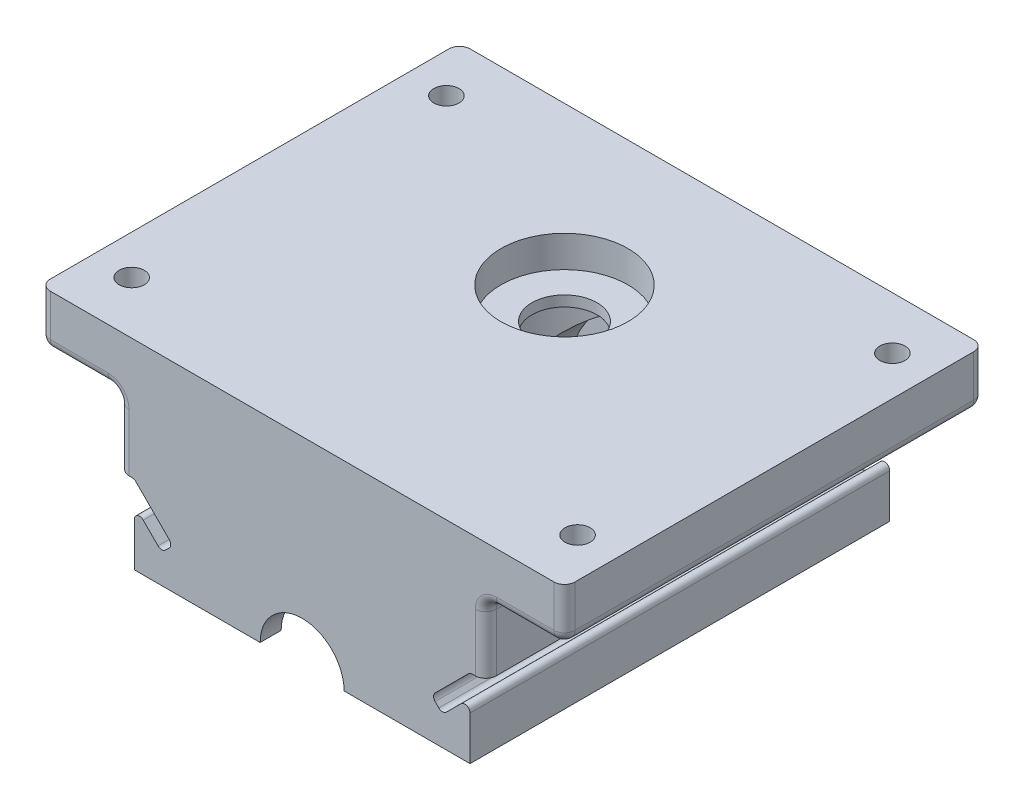
SolidWorks part; units mm, degrees
ref_plane "Plan de face" through (0, 0, 0) normal (0, 0, 1) x (1, 0, 0)
ref_plane "Plan de dessus" through (0, 0, 0) normal (0, 1, 0) x (1, 0, 0)
ref_plane "Plan de droite" through (0, 0, 0) normal (1, 0, 0) x (0, 0, -1)
sketch "Esquisse1" plane through (0, 0, 0) normal (0, 1, 0) x (1, 0, 0)
  line L1 (0, 0) -> (100, 0)
  line L2 (0, 0) -> (0, 80)
  line L3 (0, 80) -> (100, 80)
  line L4 (100, 0) -> (100, 80)
  dimension "D1" = 80
  dimension "D2" = 100
extrude "Boss.-Extru.1" add sketch "Esquisse1" along normal blind 10
sketch "Esquisse2" plane through (0, 0, 0) normal (0, -1, 0) x (1, 0, 0)
  line L0 (0, -80) -> (100, -80) construction
  line L1 (15, -80) -> (85, -80)
  line L2 (15, -80) -> (15, 0)
  line L3 (15, 0) -> (85, 0)
  line L4 (85, -80) -> (85, 0)
  line L5 (0, 0) -> (100, 0) construction
  line L6 (0, 0) -> (0, -80) construction
  dimension "D1" = 15
  dimension "D2" = 70
extrude "Boss.-Extru.2" add sketch "Esquisse2" along normal blind 28
sketch "Esquisse11" plane through (0, 0, -80) normal (0, 0, -1) x (-1, 0, 0)
  line L0 (-15, -28) -> (-85, -28) construction
  line L1 (-15, -28) -> (-85, -28)
  line L2 (-15, -28) -> (-85, -28) construction
  circle A0 centre (-50, -28) radius 20
  point P7 (-50, -28)
  dimension "D1" = 40
extrude "Boss.-Extru.3" add sketch "Esquisse11" along normal blind 6.15 contours L1 A0
sketch "Esquisse3" plane through (0, -28, -30) normal (0, 1, 0) x (1, 0, 0)
  line L0 (50, 56.15) -> (50, -30)
  line L4 (50, 52.15) -> (62, 52.15)
  line L5 (50, 52.15) -> (50, 45.95)
  line L6 (50, 45.95) -> (62, 45.95)
  line L7 (62, 52.15) -> (62, 45.95)
  line L8 (50, 45.95) -> (58, 45.95)
  line L9 (50, 45.95) -> (50, 41.95)
  line L10 (50, 41.95) -> (58, 41.95)
  line L11 (58, 45.95) -> (58, 41.95)
  line L12 (50, 41.95) -> (71.5, 41.95)
  line L13 (50, 41.95) -> (50, -15.8)
  line L14 (50, -15.8) -> (71.5, -15.8)
  line L15 (71.5, 41.95) -> (71.5, -15.8)
  line L16 (50, -19.8) -> (58, -19.8)
  line L17 (50, -19.8) -> (50, -15.8)
  line L18 (50, -15.8) -> (58, -15.8)
  line L19 (58, -19.8) -> (58, -15.8)
  line L20 (50, -26) -> (62, -26)
  line L21 (50, -26) -> (50, -19.8)
  line L22 (50, -19.8) -> (62, -19.8)
  line L23 (62, -26) -> (62, -19.8)
  line L24 (50, -30) -> (58, -30)
  line L25 (50, -30) -> (50, -26)
  line L26 (50, -26) -> (58, -26)
  line L27 (58, -30) -> (58, -26)
  line L31 (15, 50) -> (15, -30)
  line L32 (30, 50) -> (15, 50)
  line L33 (85, -30) -> (85, 50)
  line L34 (15, -30) -> (85, -30)
  line L35 (15, 50) -> (15, -30)
  line L36 (30, 50) -> (15, 50)
  line L37 (85, -30) -> (85, 50)
  line L38 (15, -30) -> (85, -30)
  line L42 (30, 56.15) -> (30, 50)
  line L43 (30, 56.15) -> (30, 50)
  line L44 (70, 56.15) -> (30, 56.15)
  line L45 (70, 56.15) -> (30, 56.15)
  line L46 (70, 50) -> (70, 56.15)
  line L47 (70, 50) -> (70, 56.15)
  line L48 (85, 50) -> (70, 50)
  line L49 (85, 50) -> (70, 50)
  line L50 (15, 50) -> (15, -30)
  line L51 (30, 50) -> (15, 50)
  line L52 (30, 56.15) -> (30, 50)
  line L53 (70, 56.15) -> (30, 56.15)
  line L54 (70, 50) -> (70, 56.15)
  line L55 (85, 50) -> (70, 50)
  line L56 (85, -30) -> (85, 50)
  line L57 (15, -30) -> (85, -30)
  line L58 (15, 50) -> (15, -30)
  line L59 (30, 50) -> (15, 50)
  line L60 (30, 56.15) -> (30, 50)
  line L61 (70, 56.15) -> (30, 56.15)
  line L62 (70, 50) -> (70, 56.15)
  line L63 (85, 50) -> (70, 50)
  line L64 (85, -30) -> (85, 50)
  line L65 (15, -30) -> (85, -30)
  point P44 (50, -30)
  dimension "D2" = 6.2
  dimension "D3" = 12
  dimension "D4" = 4
  dimension "D5" = 8
  dimension "D6" = 4
  dimension "D7" = 4
  dimension "D8" = 8
  dimension "D9" = 6.2
  dimension "D10" = 12
  dimension "D11" = 8
  dimension "D12" = 21.5
  dimension "D14" = 0
  dimension "D15" = 4
  dimension "D13" = 0
revolve "Enlèvement de matière-Révolution1" cut sketch "Esquisse3" angle 360 about L0
sketch "Esquisse4" plane through (0, -28, 0) normal (0, -1, 0) x (-1, 0, 0)
  line L0 (-58, 0) -> (-58, 4) construction
  line L1 (-58, 4) -> (-62, 4) construction
  line L2 (-62, 4) -> (-62, 10.2) construction
  line L3 (-62, 10.2) -> (-58, 10.2) construction
  line L4 (-58, 10.2) -> (-58, 14.2) construction
  line L5 (-58, 14.2) -> (-71.5, 14.2) construction
  line L6 (-71.5, 71.95) -> (-58, 71.95) construction
  line L7 (-58, 71.95) -> (-58, 75.95) construction
  line L8 (-58, 75.95) -> (-62, 75.95) construction
  line L9 (-62, 75.95) -> (-62, 82.15) construction
  line L10 (-62, 82.15) -> (-38, 82.15) construction
  line L11 (-38, 82.15) -> (-38, 75.95) construction
  line L12 (-38, 75.95) -> (-42, 75.95) construction
  line L13 (-42, 75.95) -> (-42, 71.95) construction
  line L14 (-42, 71.95) -> (-28.5, 71.95) construction
  line L15 (-28.5, 14.2) -> (-42, 14.2) construction
  line L16 (-42, 14.2) -> (-42, 10.2) construction
  line L17 (-42, 10.2) -> (-38, 10.2) construction
  line L18 (-38, 10.2) -> (-38, 4) construction
  line L19 (-38, 4) -> (-42, 4) construction
  line L20 (-42, 4) -> (-42, 0) construction
  line L21 (-42, 0) -> (-15, 0) construction
  line L22 (-15, 0) -> (-15, 80) construction
  line L23 (-50, 14.2) -> (-50, 86.15)
  line L24 (-85, 80) -> (-85, 0) construction
  line L25 (-85, 0) -> (-58, 0) construction
  line L26 (-28.5, 14.2) -> (-71.5, 14.2) construction
  line L27 (-71.5, 71.95) -> (-28.5, 71.95) construction
  line L28 (-58, 0) -> (-58, 4)
  line L29 (-58, 4) -> (-62, 4)
  line L30 (-62, 4) -> (-62, 10.2)
  line L31 (-62, 10.2) -> (-58, 10.2)
  line L32 (-58, 10.2) -> (-58, 14.2)
  line L33 (-58, 14.2) -> (-71.5, 14.2)
  line L34 (-71.5, 71.95) -> (-58, 71.95)
  line L35 (-58, 71.95) -> (-58, 75.95)
  line L36 (-58, 75.95) -> (-62, 75.95)
  line L37 (-62, 75.95) -> (-62, 82.15)
  line L38 (-62, 82.15) -> (-38, 82.15)
  line L39 (-38, 82.15) -> (-38, 75.95)
  line L40 (-38, 75.95) -> (-42, 75.95)
  line L41 (-42, 75.95) -> (-42, 71.95)
  line L42 (-42, 71.95) -> (-28.5, 71.95)
  line L43 (-28.5, 14.2) -> (-42, 14.2)
  line L44 (-42, 14.2) -> (-42, 10.2)
  line L45 (-42, 10.2) -> (-38, 10.2)
  line L46 (-38, 10.2) -> (-38, 4)
  line L47 (-38, 4) -> (-42, 4)
  line L48 (-42, 4) -> (-42, 0)
  line L49 (-42, 0) -> (-15, 0)
  line L50 (-15, 0) -> (-15, 80)
  line L51 (-15, 80) -> (-85, 80)
  line L52 (-85, 80) -> (-85, 0)
  line L53 (-85, 0) -> (-58, 0)
  line L54 (-28.5, 14.2) -> (-71.5, 14.2)
  line L55 (-71.5, 71.95) -> (-28.5, 71.95)
  line L57 (-30, 86.15) -> (-30, 80) construction
  line L58 (-70, 86.15) -> (-30, 86.15) construction
  line L59 (-70, 86.15) -> (-70, 80) construction
  line L60 (-30, 86.15) -> (-30, 80)
  line L61 (-70, 86.15) -> (-30, 86.15)
  line L62 (-70, 86.15) -> (-70, 80)
  circle A0 centre (-50, 50) radius 21
  dimension "D1" = 42
  dimension "D2" = 30
extrude "Enlèv. mat.-Extru.1" cut sketch "Esquisse4" against normal blind 30
sketch "Esquisse5" plane through (0, 10, 0) normal (0, 1, 0) x (1, 0, 0)
  line L0 (50, 80) -> (50, 0)
  line L4 (0, 0) -> (100, 0)
  line L5 (100, 0) -> (100, 80)
  line L6 (100, 80) -> (0, 80)
  line L7 (0, 80) -> (0, 0)
  line L8 (0, 0) -> (100, 0)
  line L9 (100, 0) -> (100, 80)
  line L10 (100, 80) -> (0, 80)
  line L11 (0, 80) -> (0, 0)
  circle A0 centre (50, 50) radius 12.1
  dimension "D2" = 24.2
  dimension "D3" = 30
  dimension "D1" = 0
extrude "Enlèv. mat.-Extru.2" cut sketch "Esquisse5" against normal blind 6
sketch "Esquisse6" plane through (0, 4, 0) normal (0, 1, 0) x (1, 0, 0)
  circle A0 centre (50, 50) radius 6.2
  circle A1 centre (50, 50) radius 12.1
  circle A2 centre (50, 50) radius 12.1
  dimension "D2" = 12.4
  dimension "D1" = 0
extrude "Enlèv. mat.-Extru.3" cut sketch "Esquisse6" against normal through all contours A0
sketch "Esquisse7" plane through (0, 0, 0) normal (0, 0, 1) x (1, 0, 0)
  line L0 (18.2929, -13.2929) -> (24.6569, -19.6569)
  line L1 (15, -28) -> (18, -28)
  line L2 (15, -28) -> (15, -13)
  line L3 (15, -13) -> (17.5858, -13)
  line L4 (18, -28) -> (18, -19.6569)
  line L5 (18, -13) -> (25.364, -20.364)
  line L7 (24.6569, -21.0711) -> (23.9497, -21.7782)
  line L8 (19.7071, -18.9497) -> (22.5355, -21.7782)
  line L9 (58, -28) -> (85, -28)
  line L10 (85, -28) -> (85, 0)
  line L11 (85, 0) -> (100, 0)
  line L12 (100, 0) -> (100, 10)
  line L13 (100, 10) -> (0, 10)
  line L14 (0, 10) -> (0, 0)
  line L15 (0, 0) -> (15, 0)
  line L16 (15, 0) -> (15, -28)
  line L17 (15, -28) -> (42, -28)
  line L18 (58, -28) -> (85, -28)
  line L20 (85, 0) -> (100, 0)
  line L21 (100, 0) -> (100, 10)
  line L22 (100, 10) -> (0, 10)
  line L23 (0, 10) -> (0, 0)
  line L24 (0, 0) -> (15, 0)
  line L25 (15, 0) -> (15, -28)
  line L26 (15, -28) -> (42, -28)
  line L27 (50, -33) -> (50, -25)
  line L28 (82, -28) -> (82, -19.6569)
  line L29 (80.2929, -18.9497) -> (77.4645, -21.7782)
  line L30 (75.3431, -21.0711) -> (76.0503, -21.7782)
  line L31 (81.7071, -13.2929) -> (75.3431, -19.6569)
  line L32 (85, -13) -> (82.4142, -13)
  arc A0 (24.6569, -19.6569) -> (24.6569, -21.0711) centre (23.9497, -20.364) cw
  arc A1 (58, -28) -> (42, -28) centre (50, -28) ccw
  arc A3 (23.9497, -21.7782) -> (22.5355, -21.7782) centre (23.2426, -21.0711) cw
  arc A4 (19.7071, -18.9497) -> (18, -19.6569) centre (19, -19.6569) ccw
  arc A5 (80.2929, -18.9497) -> (82, -19.6569) centre (81, -19.6569) cw
  arc A6 (76.0503, -21.7782) -> (77.4645, -21.7782) centre (76.7574, -21.0711) ccw
  arc A7 (75.3431, -19.6569) -> (75.3431, -21.0711) centre (76.0503, -20.364) ccw
  arc A8 (18.2929, -13.2929) -> (17.5858, -13) centre (17.5858, -14) ccw
  arc A9 (81.7071, -13.2929) -> (82.4142, -13) centre (82.4142, -14) cw
  arc A11 (58, -28) -> (42, -28) centre (50, -28) ccw
  point P43 (82, -13)
  dimension "D7" = 1
  dimension "D8" = 1
  dimension "D3" = 1
  dimension "D11" = 1
  dimension "D2" = 15
  dimension "D4" = 9
  dimension "D5" = 45
  dimension "D6" = 3
  dimension "D9" = 8.3431
  dimension "D10" = 3
  dimension "D1" = 0
extrude "Enlèv. mat.-Extru.5" cut sketch "Esquisse7" against normal through all
sketch "Esquisse8" plane through (0, 0, 0) normal (0, -1, 0) x (1, 0, 0)
  line L0 (7.5, 0) -> (7.5, -80)
  line L1 (0, 0) -> (15, 0) construction
  line L2 (0, -80) -> (15, -80) construction
  line L3 (92.5, 0) -> (92.5, -80)
  line L4 (85, 0) -> (100, 0) construction
  line L5 (85, -80) -> (100, -80) construction
  point P6 (7.5, -10)
  point P7 (7.5, -70)
  point P14 (92.5, -10)
  point P15 (92.5, -70)
  dimension "D1" = 10
  dimension "D2" = 10
  dimension "D3" = 10
  dimension "D4" = 10
hole_wizard "Chambrage pour vis à six pans creux M41" positions "Esquisse3D1" profile "Esquisse9" counterbore size "M4" standard "ISO" end condition through all
sketch3d "Esquisse3D1"
  point P0 (7.5, 0, -10)
  point P3 (7.5, 0, -70)
  point P6 (92.5, 0, -70)
  point P9 (92.5, 0, -10)
sketch "Esquisse9" plane through (7.5, 0, -10) normal (1, 0, 0) x (0, 0, -1)
  line L0 (0, 0) -> (0, 10)
  line L1 (0, 10) -> (2.4, 10)
  line L3 (2.4, 10) -> (2.4, 4.4)
  line L4 (2.4, 4.4) -> (4, 4.4)
  line L5 (4, 4.4) -> (4, 0)
  line L7 (4, 0) -> (0, 0)
  line L11 (0, -6.35) -> (0, 107.95) construction
  dimension "Diamètre du perçage jusqu'au prochain" = 4.8
  dimension "Profondeur du perçage jusqu'au prochain" = 10
  dimension "Diamètre du chambrage" = 8
  dimension "Profondeur du chambrage" = 4.4
fillet "Congé1" radius 2 18 edges at (50, -8, -86.15) (50, -8, -80) (15, -6.5, 0) (7.5, 0, 0) (0, 5, 0) (100, 5, 0) (92.5, 0, 0) (85, -6.5, 0) (85, -6.5, -80) (92.5, 0, -80) (100, 5, -80) (0, 5, -80) (7.5, 0, -80) (15, -6.5, -80) (100, 0, -40) (0, 0, -40) (85, 0, -40) (15, 0, -40)
